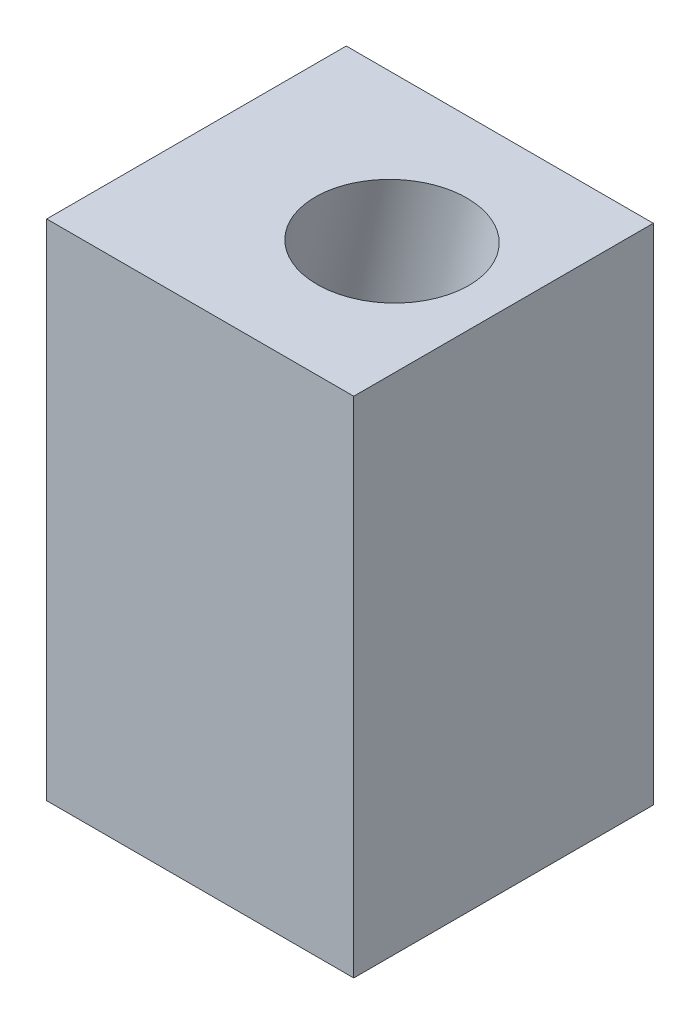
SolidWorks part; units mm, degrees
material "1060 Alloy"
ref_plane "Front Plane" through (0, 0, 0) normal (0, 0, 1) x (1, 0, 0)
ref_plane "Top Plane" through (0, 0, 0) normal (0, 1, 0) x (1, 0, 0)
ref_plane "Right Plane" through (0, 0, 0) normal (1, 0, 0) x (0, 0, -1)
sketch "Sketch1" plane through (0, 0, 0) normal (0, 0, 1) x (1, 0, 0)
  line L1 (-13.0175, -21.3614) -> (13.0175, -21.3614)
  line L2 (-13.0175, -21.3614) -> (-13.0175, 21.3614)
  line L3 (-13.0175, 21.3614) -> (13.0175, 21.3614)
  line L4 (13.0175, -21.3614) -> (13.0175, 21.3614)
  line L5 (-13.0175, -21.3614) -> (13.0175, 21.3614) construction
  line L6 (-13.0175, 21.3614) -> (13.0175, -21.3614) construction
  point P0 (0, 0)
  dimension "D1" = 42.7228
  dimension "D2" = 26.035
extrude "Boss-Extrude1" add sketch "Sketch1" along normal blind 25.4
sketch "Sketch18" plane through (0, 0, 25.4) normal (0, 0, 1) x (1, 0, 0)
  line L0 (13.0175, 21.3614) -> (-11.3408, 26.7615) construction
  line L1 (13.0175, 21.3614) -> (-13.0175, 21.3614) construction
  dimension "D1" = 12.5
ref_plane "Plane1" through (5.1237, 23.1114, 0) normal (-0.2164, -0.9763, 0) x (-0.9763, 0.2164, 0)
sketch "Sketch19" plane through (5.1237, 23.1114, 0) normal (-0.2164, -0.9763, 0) x (-0.9763, 0.2164, 0)
  line L0 (-8.0855, -25.4) -> (-8.0855, 0) construction
  circle A0 centre (1.4395, -12.3972) radius 6.35
  dimension "D1" = 12.7
  dimension "D2" = 9.525
extrude "Cut-Extrude1" cut sketch "Sketch19" along normal blind 31.75 contours A0
